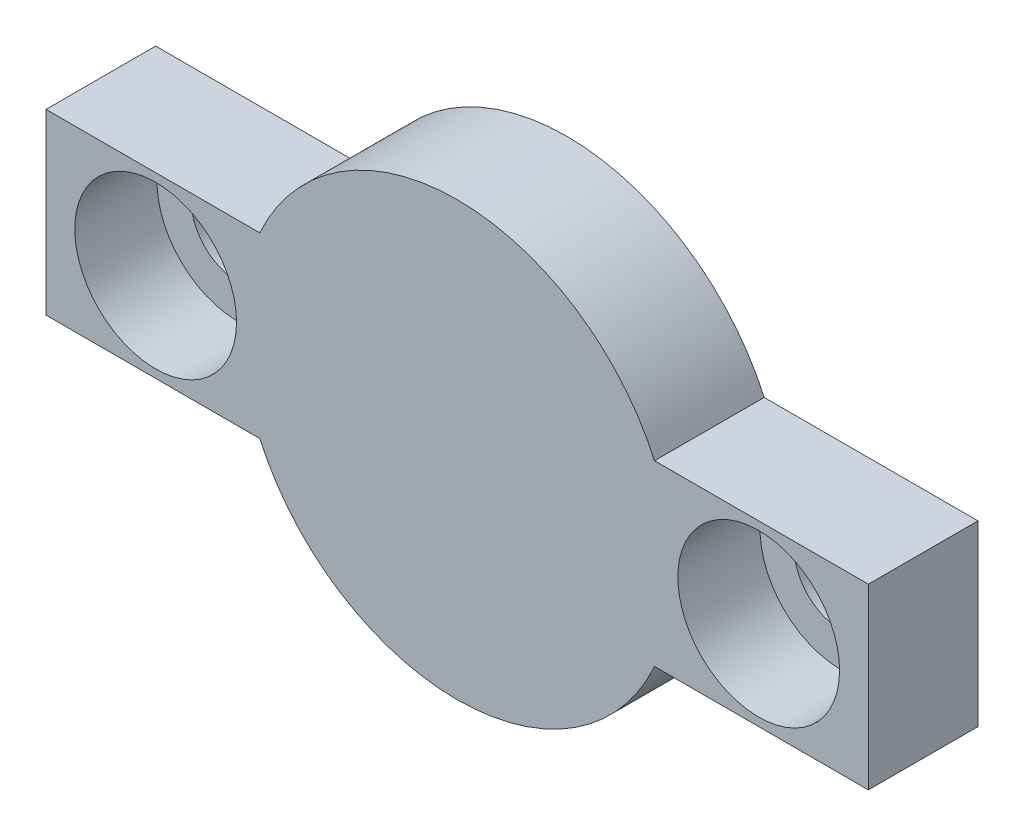
SolidWorks part; units mm, degrees
material "PLA"
ref_plane "Alzado" through (0, 0, 0) normal (0, 0, 1) x (1, 0, 0)
ref_plane "Planta" through (0, 0, 0) normal (0, 1, 0) x (1, 0, 0)
ref_plane "Vista lateral" through (0, 0, 0) normal (1, 0, 0) x (0, 0, -1)
sketch "Croquis1" plane through (0, 0, 0) normal (0, 0, 1) x (1, 0, 0)
  line L0 (-7.2005, -3.25) -> (-15, -3.25)
  line L1 (15, -3.25) -> (7.2005, -3.25)
  line L2 (15, -3.25) -> (15, 3.25)
  line L3 (15, 3.25) -> (7.2005, 3.25)
  line L4 (-15, -3.25) -> (-15, 3.25)
  line L5 (15, -3.25) -> (-15, 3.25) construction
  line L6 (15, 3.25) -> (-15, -3.25) construction
  line L7 (-7.2005, 3.25) -> (-15, 3.25)
  arc A2 (7.2005, 3.25) -> (-7.2005, 3.25) centre (0, 0) ccw
  arc A4 (-7.2005, -3.25) -> (7.2005, -3.25) centre (0, 0) ccw
  dimension "D3" = 7.9
  dimension "D1" = 6.5
  dimension "D2" = 30
extrude "Saliente-Extruir1" add sketch "Croquis1" along normal blind 4
sketch "Croquis2" plane through (0, 0, 4) normal (0, 0, 1) x (1, 0, 0)
  line L0 (-11, 0) -> (11, 0) construction
  circle A0 centre (-11, 0) radius 1.7
  circle A1 centre (11, 0) radius 1.7
  point P3 (0, 0)
  dimension "D1" = 3.4
  dimension "D2" = 22
extrude "Cortar-Extruir1" cut sketch "Croquis2" against normal blind 4
sketch "Croquis3" plane through (0, 0, 4) normal (0, 0, 1) x (1, 0, 0)
  circle A0 centre (-11, 0) radius 2.95
  circle A1 centre (11, 0) radius 2.95
  dimension "D1" = 5.9
extrude "Cortar-Extruir2" cut sketch "Croquis3" against normal blind 3
